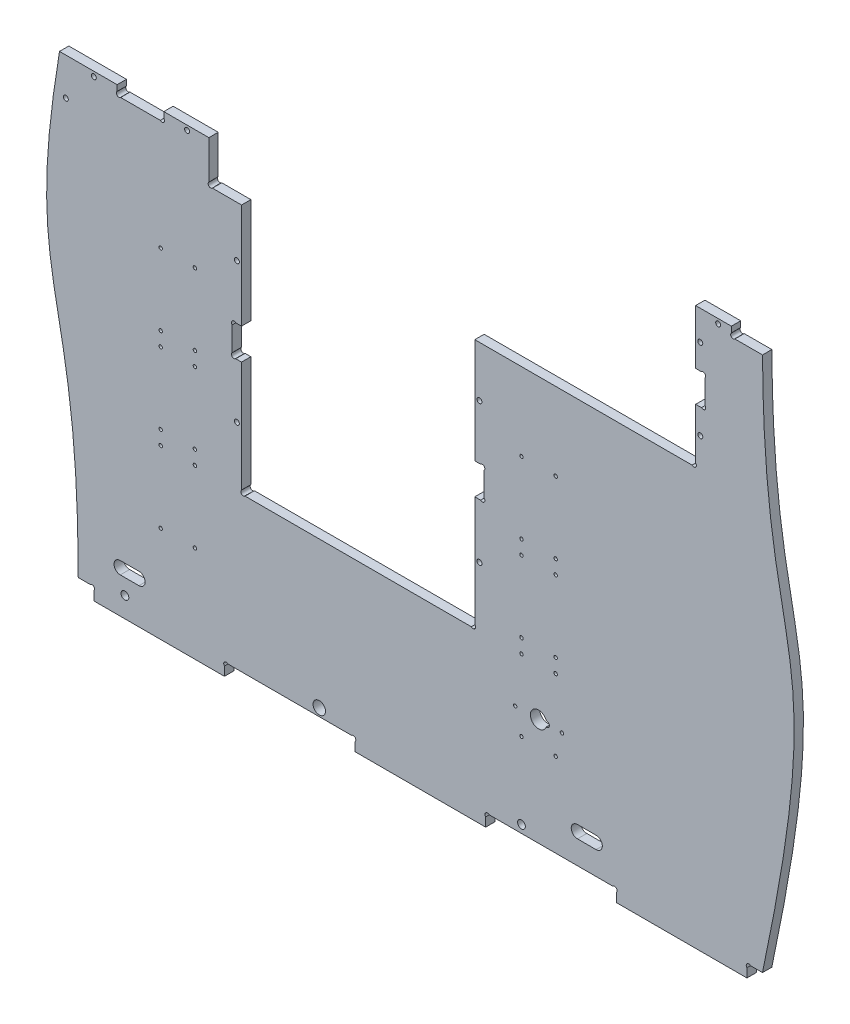
SolidWorks part; units mm, degrees
ref_plane "Plan de face" through (0, 0, 0) normal (0, 0, 1) x (1, 0, 0)
ref_plane "Plan de dessus" through (0, 0, 0) normal (0, 1, 0) x (1, 0, 0)
ref_plane "Plan de droite" through (0, 0, 0) normal (1, 0, 0) x (0, 0, -1)
sketch "Esquisse1" plane through (0, 0, 0) normal (0, 0, 1) x (1, 0, 0)
  line L0 (536.5085, 0) -> (-13.3743, 0) construction
  line L1 (0, 0) -> (84, 0)
  line L2 (0, 8) -> (-13.4384, -5.4384) construction
  line L3 (74, 299.7492) -> (74, 264.55) construction
  line L4 (-10, 8) -> (-2.2627, 8)
  line L5 (401.5, 343.0641) -> (401.5, 360.8026) construction
  line L6 (420, -67.8064) -> (420, 420.4252) construction
  line L7 (-58.7504, 358) -> (536.5085, 358) construction
  line L8 (-44.4443, 8) -> (504.1642, 8) construction
  line L9 (-58.7504, 183) -> (504.1642, 183) construction
  line L10 (210, -34.4525) -> (210, 403.8703) construction
  line L11 (95, 312.8184) -> (95, 62.6795) construction
  line L12 (245, 312.8184) -> (245, 13.5522) construction
  line L13 (44.0199, 268) -> (399.1636, 268) construction
  line L14 (81.9912, 113) -> (257.0223, 113) construction
  line L15 (170, 297.7251) -> (170, 173.0003) construction
  line L16 (387, 358) -> (410, 358)
  line L17 (384.7373, 268) -> (245, 268)
  line L18 (50.7262, 190.5) -> (129.5539, 190.5) construction
  line L19 (81.9912, 180.5) -> (97.9919, 180.5) construction
  line L20 (89, 328.4277) -> (89, 62.6795) construction
  line L21 (89, 180.5) -> (106.3802, 197.8802) construction
  line L22 (112.0092, 188) -> (102.8156, 188) construction
  line L23 (95, 268) -> (76.2627, 268)
  line L24 (387, 358) -> (387, 323)
  line L25 (81.9912, 145.5) -> (97.9919, 145.5) construction
  line L26 (92, 278.6686) -> (92, 94.6559) construction
  line L27 (112.0092, 284) -> (81.9912, 284) construction
  line L28 (387, 303) -> (387, 270.2627)
  line L29 (91.2627, 180.5) -> (95, 180.5)
  line L30 (95, 180.5) -> (95, 109.2627)
  line L31 (95, 200.5) -> (95, 268)
  line L32 (91.2627, 200.5) -> (95, 200.5)
  line L33 (89, 198.2373) -> (89, 182.7627)
  line L34 (407.4079, 352) -> (432.4166, 352) construction
  line L35 (74, 295) -> (74, 270.2627)
  line L36 (297, 44.5756) -> (297, 252.237) construction
  line L37 (251, 198.2373) -> (251, 182.7627)
  line L38 (248.7373, 200.5) -> (245, 200.5)
  line L39 (245, 200.5) -> (245, 268)
  line L40 (245, 180.5) -> (245, 109.2627)
  line L41 (248.7373, 180.5) -> (245, 180.5)
  line L42 (81.9912, 107) -> (257.0223, 107) construction
  line L43 (97.2627, 107) -> (242.7373, 107)
  line L44 (84, 13) -> (84, -67.8064) construction
  line L45 (168, 13.5522) -> (168, -67.8064) construction
  line L46 (126, 13.5522) -> (126, -34.4525) construction
  line L47 (84, 8) -> (114.9336, -22.9336) construction
  line L48 (86.2627, 8) -> (165.7373, 8)
  line L49 (84, 5.7373) -> (84, 0)
  line L50 (168, 5.7373) -> (168, 0)
  line L51 (252, 5.7373) -> (252, 0)
  line L52 (168, 0) -> (252, 0)
  line L53 (336, 5.7373) -> (336, 0)
  line L54 (333.7373, 8) -> (254.2627, 8)
  line L55 (336, 0) -> (420, 0)
  line L56 (-18, 278.6686) -> (-18, 232.7276) construction
  line L57 (357.3411, 339) -> (411.7088, 339) construction
  line L58 (15, 295) -> (-22.0608, 295)
  line L59 (-30, -67.8064) -> (-30, 412.0672) construction
  line L60 (-10, 374.1921) -> (-10, -22.9336) construction
  line L61 (-20, 196.1893) -> (-20, 121.5026) construction
  line L62 (410, 352) -> (421.6263, 363.6263) construction
  line L63 (-44.4443, 158) -> (15.8377, 158) construction
  line L64 (-58.7504, 208) -> (12.2974, 208) construction
  line L65 (430.0159, 352) -> (412.2627, 352)
  line L66 (420, 0) -> (420, 5.7373)
  line L67 (422.2627, 8) -> (430, 8)
  line L68 (420, 8) -> (436.9027, -8.9027) construction
  line L69 (0, 5.7373) -> (0, 0)
  line L70 (401.5, 323) -> (357.3411, 323) construction
  line L71 (357.3411, 303) -> (411.7088, 303) construction
  line L72 (357.3411, 287) -> (411.7088, 287) construction
  line L73 (375.1527, 313) -> (400.9535, 313) construction
  line L74 (410, 354.2627) -> (410, 358)
  line L75 (387, -22.9336) -> (387, 364.1831) construction
  line L76 (393, 246.4699) -> (393, 324.4458) construction
  line L77 (387, 303) -> (396.2728, 312.2728) construction
  line L78 (387, 323) -> (390.7373, 323)
  line L79 (393, 320.7373) -> (393, 305.2627)
  line L80 (430, 429.0413) -> (430, 142.9931) construction
  line L81 (390, 390.6781) -> (390, 264.55) construction
  line L82 (390.7373, 303) -> (387, 303)
  line L83 (74, 295) -> (45, 295)
  line L84 (95, 107) -> (145.4679, 157.4679) construction
  line L85 (275, 252.237) -> (275, 44.5756) construction
  line L86 (310.9651, 62) -> (218.1134, 62) construction
  line L87 (310.9651, 108) -> (269.3118, 108) construction
  line L88 (410, 378.6044) -> (410, 349.1334) construction
  line L89 (404.9347, 355) -> (378.0532, 355) construction
  line L90 (310.9651, 117) -> (269.3118, 117) construction
  line L91 (286, 140) -> (310.9651, 140) construction
  line L92 (74, 268) -> (89.587, 283.587) construction
  line L93 (387, 268) -> (367.9677, 287.0323) construction
  line L94 (317, 34.254) -> (317, -22.9336) construction
  line L95 (311, 34.254) -> (311, -22.9336) construction
  line L96 (334.4217, 27) -> (304.8576, 27) construction
  line L97 (344.2001, 23) -> (299.3026, 23) construction
  line L98 (344.2001, 31) -> (299.3026, 31) construction
  line L99 (323, 31) -> (311, 31)
  line L100 (323, 23) -> (311, 23)
  line L101 (20, -22.9336) -> (20, 31) construction
  line L102 (-24.9818, 13) -> (454.5584, 13) construction
  line L103 (29, 23) -> (17, 23)
  line L104 (29, 31) -> (17, 31)
  line L105 (367.9677, 77) -> (218.1134, 77) construction
  line L106 (286, 88.7776) -> (286, 65.2617) construction
  line L107 (291.2, 82.8223) -> (291.2, 70.657) construction
  line L108 (291.2, 78.75) -> (290.9497, 78.75)
  line L109 (291.2, 75.25) -> (290.9497, 75.25)
  line L110 (280.75, 77) -> (280.75, 84.0033) construction
  line L111 (292.95, 77) -> (292.95, 84.0033) construction
  line L114 (-27.2619, 295) -> (81.9912, 295) construction
  line L115 (73, 282.5821) -> (73, 374.1921) construction
  line L116 (-27.2619, 289) -> (81.9912, 289) construction
  line L117 (30, 312.8686) -> (30, 284) construction
  line L118 (45, 309) -> (45, 284) construction
  line L119 (45, 289) -> (31.8516, 302.1484) construction
  line L120 (60, 309) -> (60, 284) construction
  line L121 (68.4592, 292) -> (52.4653, 292) construction
  line L122 (15, 295) -> (15, 291.2627)
  line L124 (17.2627, 289) -> (42.7373, 289)
  line L125 (45, 295) -> (45, 291.2627)
  circle A0 centre (401.5, 355) radius 1.6
  arc A1 (410, 354.2627) -> (412.2627, 352) centre (411.1314, 353.1314) ccw
  arc A2 (89, 182.7627) -> (91.2627, 180.5) centre (90.1314, 181.6314) ccw
  circle A3 centre (92, 145.5) radius 1.6
  arc A4 (89, 198.2373) -> (91.2627, 200.5) centre (90.1314, 199.3686) cw
  circle A5 centre (92, 235.5) radius 1.6
  circle A6 centre (275, 62) radius 1.1
  circle A7 centre (297, 62) radius 1.1
  circle A8 centre (248, 235.5) radius 1.6
  arc A9 (251, 198.2373) -> (248.7373, 200.5) centre (249.8686, 199.3686) ccw
  circle A10 centre (248, 145.5) radius 1.6
  arc A11 (251, 182.7627) -> (248.7373, 180.5) centre (249.8686, 181.6314) cw
  arc A12 (86.2627, 8) -> (84, 5.7373) centre (85.1314, 6.8686) ccw
  arc A13 (165.7373, 8) -> (168, 5.7373) centre (166.8686, 6.8686) cw
  arc A14 (254.2627, 8) -> (252, 5.7373) centre (253.1314, 6.8686) ccw
  arc A15 (333.7373, 8) -> (336, 5.7373) centre (334.8686, 6.8686) cw
  circle A16 centre (297, 108) radius 1.1
  circle A17 centre (275, 108) radius 1.1
  circle A18 centre (-18, 271) radius 1.6
  arc A19 (422.2627, 8) -> (420, 5.7373) centre (421.1314, 6.8686) ccw
  arc A20 (0, 5.7373) -> (-2.2627, 8) centre (-1.1314, 6.8686) ccw
  circle A21 centre (275, 117) radius 1.1
  arc A22 (393, 305.2627) -> (390.7373, 303) centre (391.8686, 304.1314) cw
  arc A23 (393, 320.7373) -> (390.7373, 323) centre (391.8686, 321.8686) ccw
  circle A24 centre (297, 117) radius 1.1
  circle A25 centre (297, 163) radius 1.1
  arc A26 (95, 109.2627) -> (97.2627, 107) centre (96.1314, 108.1314) ccw
  circle A27 centre (390, 339) radius 1.6
  circle A28 centre (390, 287) radius 1.6
  arc A29 (245, 109.2627) -> (242.7373, 107) centre (243.8686, 108.1314) cw
  circle A30 centre (275, 163) radius 1.1
  circle A31 centre (275, 172) radius 1.1
  circle A32 centre (297, 172) radius 1.1
  circle A33 centre (297, 218) radius 1.1
  circle A34 centre (275, 218) radius 1.1
  arc A35 (384.7373, 268) -> (387, 270.2627) centre (385.8686, 269.1314) ccw
  arc A36 (74, 270.2627) -> (76.2627, 268) centre (75.1314, 269.1314) ccw
  arc A37 (311, 31) -> (311, 23) centre (311, 27) ccw
  arc A38 (323, 31) -> (323, 23) centre (323, 27) cw
  circle A39 centre (20, 13) radius 2.5
  circle A40 centre (43, 62) radius 1.1
  circle A41 centre (65, 62) radius 1.1
  circle A42 centre (43, 117) radius 1.1
  circle A43 centre (65, 117) radius 1.1
  circle A44 centre (65, 108) radius 1.1
  circle A45 centre (43, 108) radius 1.1
  circle A46 centre (43, 172) radius 1.1
  circle A47 centre (65, 172) radius 1.1
  circle A48 centre (65, 163) radius 1.1
  circle A49 centre (43, 163) radius 1.1
  circle A50 centre (65, 218) radius 1.1
  circle A51 centre (43, 218) radius 1.1
  arc A52 (29, 31) -> (29, 23) centre (29, 27) cw
  arc A53 (17, 31) -> (17, 23) centre (17, 27) ccw
  circle A54 centre (145, 13) radius 4
  circle A55 centre (275, 13) radius 2.5
  circle A56 centre (60, 292) radius 1.6
  arc A57 (42.7373, 289) -> (45, 291.2627) centre (43.8686, 290.1314) ccw
  circle A58 centre (301, 77) radius 1.1
  circle A59 centre (0, 292) radius 1.6
  circle A60 centre (271, 77) radius 1.1
  arc A61 (17.2627, 289) -> (15, 291.2627) centre (16.1314, 290.1314) cw
  arc A63 (291.2, 75.25) -> (291.2, 78.75) centre (291.2, 77) ccw
  arc A64 (290.9497, 78.75) -> (290.9497, 75.25) centre (286, 77) ccw
  spline S0 degree 3 poles (-22.0608, 295) (-46.1494, 150.2196) (-10, 174.6109) (-10, 8) knots 0.111212 0.111212 0.111212 0.111212 1 1 1 1
  spline S2 degree 3 poles (430, 8) (475.2669, 222.5286) (430.9795, 171.6853) (430.0159, 352) knots 0 0 0 0 0.989181 0.989181 0.989181 0.989181
  dimension "D19" = 3
  dimension "D22" = 6
  dimension "D27" = 1
  dimension "D30" = 46
  dimension "D36" = 45
  dimension "D37" = 16
  dimension "D43" = 6
  dimension "D46" = 9
  dimension "D48" = 23
  dimension "D52" = 45
  dimension "D13" = 83
  dimension "D21" = 110
  dimension "D42" = 10
  dimension "D53" = 45
  dimension "D60" = 5
  dimension "D61" = 6
  dimension "D68" = 77
  dimension "D16" = 20
  dimension "D18" = 45
  dimension "D51" = 45
  dimension "D54" = 6
  dimension "D59" = 30
  dimension "D62" = 8
  dimension "D70" = 2.2
  dimension "D71" = 3.5
  dimension "D1" = 8
  dimension "D2" = 358
  dimension "D3" = 155
  dimension "D4" = 150
  dimension "D6" = 96
  dimension "D7" = 175
  dimension "D8" = 175
  dimension "D9" = 90
  dimension "D10" = 75
  dimension "D11" = 77.5
  dimension "D12" = 10
  dimension "D14" = 8.5
  dimension "D15" = 6
  dimension "D17" = 35
  dimension "D20" = 45
  dimension "D23" = 84
  dimension "D24" = 42
  dimension "D25" = 42
  dimension "D26" = 45
  dimension "D28" = 22
  dimension "D29" = 19
  dimension "D31" = 20
  dimension "D32" = 10
  dimension "D33" = 150
  dimension "D34" = 150
  dimension "D35" = 45
  dimension "D38" = 20
  dimension "D39" = 16
  dimension "D40" = 40
  dimension "D41" = 6
  dimension "D44" = 3
  dimension "D45" = 45
  dimension "D47" = 3
  dimension "D49" = 54
  dimension "D50" = 30
  dimension "D55" = 70
  dimension "D56" = 8
  dimension "D57" = 4
  dimension "D58" = 15
  dimension "D63" = 15
  dimension "D64" = 43
  dimension "D65" = 15
  dimension "D66" = 3
  dimension "D67" = 45
  dimension "D69" = 11
extrude "Boss.-Extru.1" add sketch "Esquisse1" along normal blind 6
